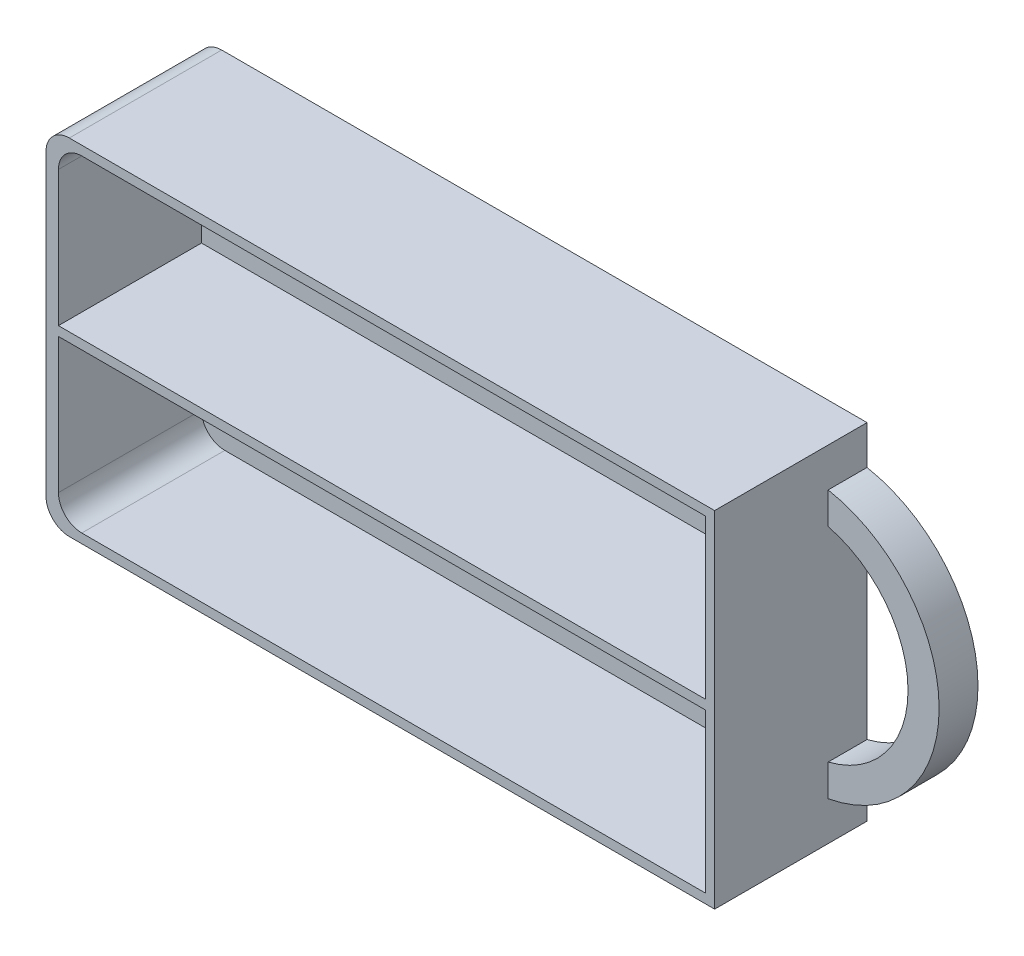
SolidWorks part; units mm, degrees
ref_plane "Спереди" through (0, 0, 0) normal (0, 0, 1) x (1, 0, 0)
ref_plane "Сверху" through (0, 0, 0) normal (0, 1, 0) x (1, 0, 0)
ref_plane "Справа" through (0, 0, 0) normal (1, 0, 0) x (0, 0, -1)
other "Configuration Table"
sketch "Эскиз1" plane through (0, 0, 0) normal (0, 0, 1) x (1, 0, 0)
  line L1 (-43, 22.2) -> (43, 22.2)
  line L2 (-43, 22.2) -> (-43, -22.2)
  line L3 (-43, -22.2) -> (43, -22.2)
  line L4 (43, 22.2) -> (43, -22.2)
  line L5 (-43, 22.2) -> (43, -22.2) construction
  line L6 (-43, -22.2) -> (43, 22.2) construction
  point P0 (0, 0)
  dimension "D1" = 86
  dimension "D2" = 44.4
extrude "Бобышка-Вытянуть1" add sketch "Эскиз1" along normal blind 19.6
sketch "Эскиз2" plane through (0, 0, 0) normal (0, 0, 1) x (1, 0, 0)
  line L0 (0, 0) -> (43, 0) construction
  line L1 (43, -22.2) -> (43, 22.2) construction
  line L2 (43, 17.2) -> (43, 13.1088)
  line L3 (43, -17.2) -> (43, -13.1088)
  arc A0 (43, -17.2) -> (43, 17.2) centre (39.7735, 0) ccw
  arc A1 (43, -13.1088) -> (43, 13.1088) centre (39.7735, 0) ccw
  dimension "D3" = 13.5
  dimension "D4" = 4
  dimension "D1" = 5
  dimension "D2" = 5
extrude "Бобышка-Вытянуть2" add sketch "Эскиз2" along normal blind 5
sketch "Эскиз3" plane through (0, 0, 19.6) normal (0, 0, 1) x (1, 0, 0)
  line L1 (41.8, 0.5971) -> (-41.4, 0.5971)
  line L2 (41.8, 0.5971) -> (41.8, -0.6029)
  line L3 (41.8, -0.6029) -> (-41.4, -0.6029)
  line L4 (-41.4, 0.5971) -> (-41.4, -0.6029)
  line L5 (-41.4, 22.2) -> (-41.4, -22.2)
  line L6 (-43, -21) -> (41.8, -21)
  line L7 (41.8, -21) -> (41.8, 21)
  line L8 (41.8, 21) -> (-43, 21)
  line L9 (-41.4, -21) -> (41.8, -21)
  line L10 (41.8, -21) -> (41.8, 21)
  line L11 (41.8, 21) -> (-41.4, 21)
  line L12 (-41.4, 21) -> (-41.4, -21)
  line L13 (41.8, 0.5971) -> (-41.4, -0.6029) construction
  line L14 (41.8, -0.6029) -> (-41.4, 0.5971) construction
  point P0 (0, 0)
  dimension "D3" = 1.2
  dimension "D4" = 20.4029
  dimension "D5" = 20.3971
  dimension "D1" = 1.2
  dimension "D2" = 1.6
extrude "Вырез-Вытянуть1" cut sketch "Эскиз3" against normal offset from surface (18.4 mm away) 1.2 contours L11 L12 L1 L10 | L3 L12 L9 L10 up to face at (48.1368, 0, 0)
fillet "Скругление1" radius 3 4 edges at (-43, 22.2, 9.8) (-43, -22.2, 9.8) (-41.4, -21, 10.4) (-41.4, 21, 10.4)
